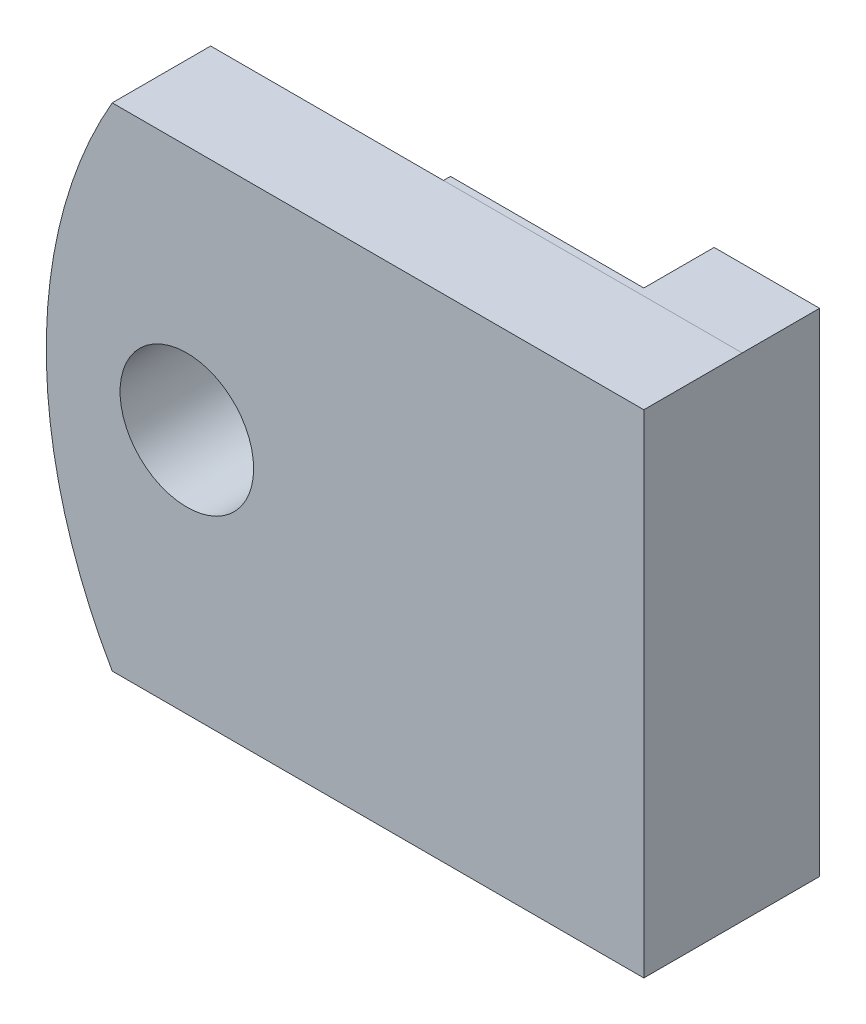
SolidWorks part; units mm, degrees
ref_plane "Front Plane" through (0, 0, 0) normal (0, 0, 1) x (1, 0, 0)
ref_plane "Top Plane" through (0, 0, 0) normal (0, 1, 0) x (1, 0, 0)
ref_plane "Right Plane" through (0, 0, 0) normal (1, 0, 0) x (0, 0, -1)
sketch "Sketch2" plane through (0, 0, 0) normal (0, 0, 1) x (1, 0, 0)
  line L6 (3, 7) -> (-12.1234, 7.0002)
  line L7 (-12.1234, -7.0002) -> (3, -7)
  line L8 (3, -7) -> (3, 7)
  arc A1 (-12.1234, 7.0002) -> (-12.1234, -7.0002) centre (-0.0013, 0) ccw
  circle A3 centre (-10, 0) radius 1.8999
  point P5 (0, 0)
  dimension "D4" = 13.9981
  dimension "D5" = 3.7998
  dimension "D1" = 15.1234
  dimension "D2" = 15.1234
  dimension "D3" = 14
  dimension "D6" = 13
extrude "Boss-Extrude1" add sketch "Sketch2" against normal blind 2.8 separate body
sketch "Sketch3" plane through (0, 0, -2.8) normal (0, 0, -1) x (-1, 0, 0)
  line L3 (-3, 7) -> (5.5, 7)
  line L4 (-3, -7) -> (5.5, -7)
  line L5 (5.5, -7) -> (5.5, 7)
  line L7 (-3, -7) -> (-3, 7)
  dimension "D1" = 8.5
  dimension "D2" = 14
  dimension "D3" = 8.5
  dimension "D4" = 14
extrude "Boss-Extrude2" add sketch "Sketch3" along normal blind 0.2
sketch "Sketch4" plane through (0, 0, -3) normal (0, 0, -1) x (-1, 0, 0)
  line L8 (-3, 7) -> (-3, -7)
  line L9 (-3, -7) -> (0, -7)
  line L10 (0, -7) -> (0, 7)
  line L11 (0, 7) -> (-3, 7)
  dimension "D1" = 14
  dimension "D2" = 3
  dimension "D3" = 14
  dimension "D4" = 3
extrude "Boss-Extrude3" add sketch "Sketch4" along normal blind 2
